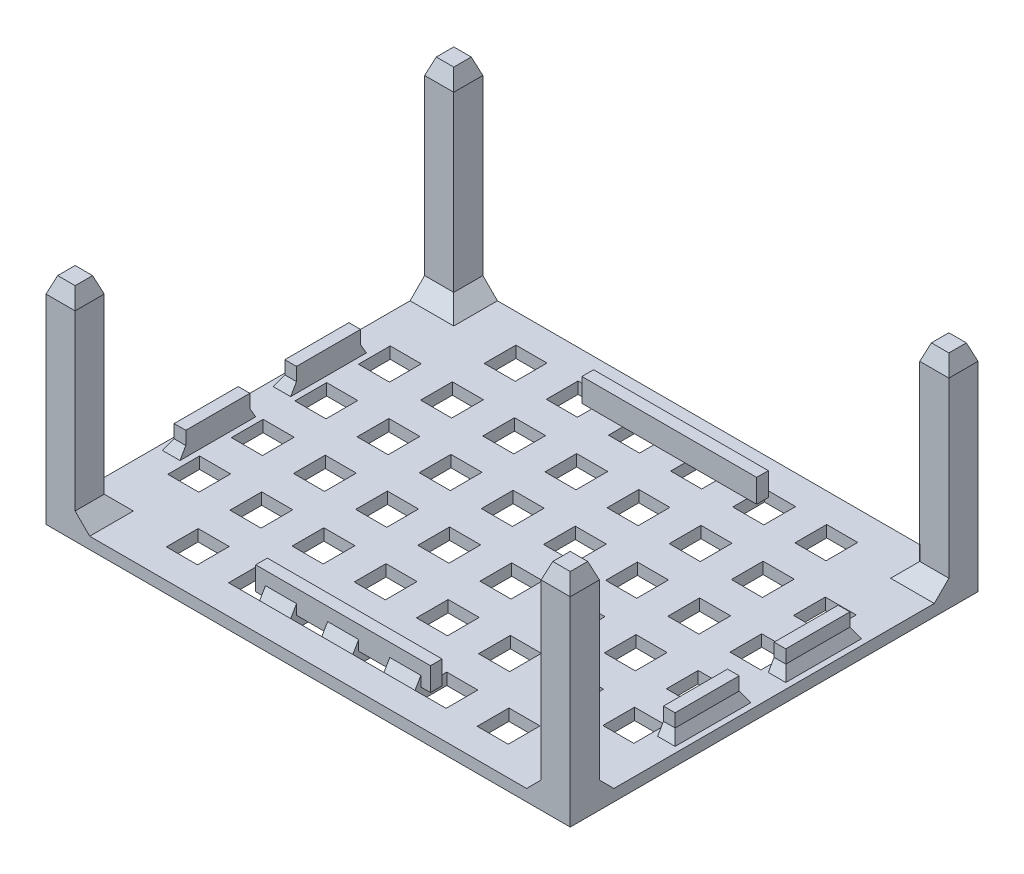
SolidWorks part; units mm, degrees
ref_plane "Plano frontal" through (0, 0, 0) normal (0, 0, 1) x (1, 0, 0)
ref_plane "Plano superior" through (0, 0, 0) normal (0, 1, 0) x (1, 0, 0)
ref_plane "Plano direito" through (0, 0, 0) normal (1, 0, 0) x (0, 0, -1)
sketch "Esboço1" plane through (0, 0, 0) normal (0, 1, 0) x (1, 0, 0)
  line L1 (-45, -35) -> (45, -35)
  line L2 (-45, -35) -> (-45, 35)
  line L3 (-45, 35) -> (45, 35)
  line L4 (45, -35) -> (45, 35)
  line L5 (-45, -35) -> (45, 35) construction
  line L6 (-45, 35) -> (45, -35) construction
  point P0 (0, 0)
  dimension "D1" = 90
  dimension "D2" = 70
extrude "Ressalto-extrusão1" add sketch "Esboço1" along normal blind 2
sketch "Esboço2" plane through (0, 2, 0) normal (0, 1, 0) x (1, 0, 0)
  line L0 (-29.33, 30) -> (-29.33, 24.55)
  line L7 (-40, 30) -> (-34.666, 30)
  line L10 (-45, 35) -> (-45, -35) construction
  line L11 (-40, -30) -> (40, -30)
  line L12 (-40, -30) -> (-40, 30)
  line L13 (-40, 30) -> (40, 30)
  line L14 (40, -30) -> (40, 30)
  line L15 (-40, -30) -> (40, 30) construction
  line L16 (-40, 30) -> (40, -30) construction
  line L17 (45, 35) -> (-45, 35) construction
  line L18 (-40, 30) -> (-40, 24.55)
  line L19 (-40, 24.55) -> (-34.666, 24.55)
  line L20 (-34.666, 30) -> (-34.666, 24.55)
  line L21 (-23.996, 30) -> (-23.996, 24.55)
  line L22 (-29.33, 30) -> (-23.996, 30)
  line L23 (-29.33, 24.55) -> (-23.996, 24.55)
  line L24 (-18.66, 30) -> (-18.66, 24.55)
  line L25 (-13.326, 30) -> (-13.326, 24.55)
  line L26 (-18.66, 30) -> (-13.326, 30)
  line L27 (-18.66, 24.55) -> (-13.326, 24.55)
  line L28 (-7.99, 30) -> (-7.99, 24.55)
  line L29 (-2.656, 30) -> (-2.656, 24.55)
  line L30 (-7.99, 30) -> (-2.656, 30)
  line L31 (-7.99, 24.55) -> (-2.656, 24.55)
  line L32 (2.68, 30) -> (2.68, 24.55)
  line L33 (8.014, 30) -> (8.014, 24.55)
  line L34 (2.68, 30) -> (8.014, 30)
  line L35 (2.68, 24.55) -> (8.014, 24.55)
  line L36 (13.35, 30) -> (13.35, 24.55)
  line L37 (18.684, 30) -> (18.684, 24.55)
  line L38 (13.35, 30) -> (18.684, 30)
  line L39 (13.35, 24.55) -> (18.684, 24.55)
  line L40 (24.02, 30) -> (24.02, 24.55)
  line L41 (29.354, 30) -> (29.354, 24.55)
  line L42 (24.02, 30) -> (29.354, 30)
  line L43 (24.02, 24.55) -> (29.354, 24.55)
  line L44 (34.69, 30) -> (34.69, 24.55)
  line L45 (40.024, 30) -> (40.024, 24.55)
  line L46 (34.69, 30) -> (40.024, 30)
  line L47 (34.69, 24.55) -> (40.024, 24.55)
  line L48 (-29.33, 19.09) -> (-29.33, 13.64)
  line L49 (-23.996, 19.09) -> (-23.996, 13.64)
  line L50 (-29.33, 19.09) -> (-23.996, 19.09)
  line L51 (-29.33, 13.64) -> (-23.996, 13.64)
  line L52 (-18.66, 19.09) -> (-18.66, 13.64)
  line L53 (-13.326, 19.09) -> (-13.326, 13.64)
  line L54 (-18.66, 19.09) -> (-13.326, 19.09)
  line L55 (-18.66, 13.64) -> (-13.326, 13.64)
  line L56 (-7.99, 19.09) -> (-7.99, 13.64)
  line L57 (-2.656, 19.09) -> (-2.656, 13.64)
  line L58 (-7.99, 19.09) -> (-2.656, 19.09)
  line L59 (-7.99, 13.64) -> (-2.656, 13.64)
  line L60 (2.68, 19.09) -> (2.68, 13.64)
  line L61 (8.014, 19.09) -> (8.014, 13.64)
  line L62 (2.68, 19.09) -> (8.014, 19.09)
  line L63 (2.68, 13.64) -> (8.014, 13.64)
  line L64 (13.35, 19.09) -> (13.35, 13.64)
  line L65 (18.684, 19.09) -> (18.684, 13.64)
  line L66 (13.35, 19.09) -> (18.684, 19.09)
  line L67 (13.35, 13.64) -> (18.684, 13.64)
  line L68 (24.02, 19.09) -> (24.02, 13.64)
  line L69 (29.354, 19.09) -> (29.354, 13.64)
  line L70 (24.02, 19.09) -> (29.354, 19.09)
  line L71 (24.02, 13.64) -> (29.354, 13.64)
  line L72 (34.69, 19.09) -> (34.69, 13.64)
  line L73 (40.024, 19.09) -> (40.024, 13.64)
  line L74 (34.69, 19.09) -> (40.024, 19.09)
  line L75 (34.69, 13.64) -> (40.024, 13.64)
  line L76 (-29.33, 8.18) -> (-29.33, 2.73)
  line L77 (-23.996, 8.18) -> (-23.996, 2.73)
  line L78 (-29.33, 8.18) -> (-23.996, 8.18)
  line L79 (-29.33, 2.73) -> (-23.996, 2.73)
  line L80 (-18.66, 8.18) -> (-18.66, 2.73)
  line L81 (-13.326, 8.18) -> (-13.326, 2.73)
  line L82 (-18.66, 8.18) -> (-13.326, 8.18)
  line L83 (-18.66, 2.73) -> (-13.326, 2.73)
  line L84 (-7.99, 8.18) -> (-7.99, 2.73)
  line L85 (-2.656, 8.18) -> (-2.656, 2.73)
  line L86 (-7.99, 8.18) -> (-2.656, 8.18)
  line L87 (-7.99, 2.73) -> (-2.656, 2.73)
  line L88 (2.68, 8.18) -> (2.68, 2.73)
  line L89 (8.014, 8.18) -> (8.014, 2.73)
  line L90 (2.68, 8.18) -> (8.014, 8.18)
  line L91 (2.68, 2.73) -> (8.014, 2.73)
  line L92 (13.35, 8.18) -> (13.35, 2.73)
  line L93 (18.684, 8.18) -> (18.684, 2.73)
  line L94 (13.35, 8.18) -> (18.684, 8.18)
  line L95 (13.35, 2.73) -> (18.684, 2.73)
  line L96 (24.02, 8.18) -> (24.02, 2.73)
  line L97 (29.354, 8.18) -> (29.354, 2.73)
  line L98 (24.02, 8.18) -> (29.354, 8.18)
  line L99 (24.02, 2.73) -> (29.354, 2.73)
  line L100 (34.69, 8.18) -> (34.69, 2.73)
  line L101 (40.024, 8.18) -> (40.024, 2.73)
  line L102 (34.69, 8.18) -> (40.024, 8.18)
  line L103 (34.69, 2.73) -> (40.024, 2.73)
  line L104 (-29.33, -2.73) -> (-29.33, -8.18)
  line L105 (-23.996, -2.73) -> (-23.996, -8.18)
  line L106 (-29.33, -2.73) -> (-23.996, -2.73)
  line L107 (-29.33, -8.18) -> (-23.996, -8.18)
  line L108 (-18.66, -2.73) -> (-18.66, -8.18)
  line L109 (-13.326, -2.73) -> (-13.326, -8.18)
  line L110 (-18.66, -2.73) -> (-13.326, -2.73)
  line L111 (-18.66, -8.18) -> (-13.326, -8.18)
  line L112 (-7.99, -2.73) -> (-7.99, -8.18)
  line L113 (-2.656, -2.73) -> (-2.656, -8.18)
  line L114 (-7.99, -2.73) -> (-2.656, -2.73)
  line L115 (-7.99, -8.18) -> (-2.656, -8.18)
  line L116 (2.68, -2.73) -> (2.68, -8.18)
  line L117 (8.014, -2.73) -> (8.014, -8.18)
  line L118 (2.68, -2.73) -> (8.014, -2.73)
  line L119 (2.68, -8.18) -> (8.014, -8.18)
  line L120 (13.35, -2.73) -> (13.35, -8.18)
  line L121 (18.684, -2.73) -> (18.684, -8.18)
  line L122 (13.35, -2.73) -> (18.684, -2.73)
  line L123 (13.35, -8.18) -> (18.684, -8.18)
  line L124 (24.02, -2.73) -> (24.02, -8.18)
  line L125 (29.354, -2.73) -> (29.354, -8.18)
  line L126 (24.02, -2.73) -> (29.354, -2.73)
  line L127 (24.02, -8.18) -> (29.354, -8.18)
  line L128 (34.69, -2.73) -> (34.69, -8.18)
  line L129 (40.024, -2.73) -> (40.024, -8.18)
  line L130 (34.69, -2.73) -> (40.024, -2.73)
  line L131 (34.69, -8.18) -> (40.024, -8.18)
  line L132 (-29.33, -13.64) -> (-29.33, -19.09)
  line L133 (-23.996, -13.64) -> (-23.996, -19.09)
  line L134 (-29.33, -13.64) -> (-23.996, -13.64)
  line L135 (-29.33, -19.09) -> (-23.996, -19.09)
  line L136 (-18.66, -13.64) -> (-18.66, -19.09)
  line L137 (-13.326, -13.64) -> (-13.326, -19.09)
  line L138 (-18.66, -13.64) -> (-13.326, -13.64)
  line L139 (-18.66, -19.09) -> (-13.326, -19.09)
  line L140 (-7.99, -13.64) -> (-7.99, -19.09)
  line L141 (-2.656, -13.64) -> (-2.656, -19.09)
  line L142 (-7.99, -13.64) -> (-2.656, -13.64)
  line L143 (-7.99, -19.09) -> (-2.656, -19.09)
  line L144 (2.68, -13.64) -> (2.68, -19.09)
  line L145 (8.014, -13.64) -> (8.014, -19.09)
  line L146 (2.68, -13.64) -> (8.014, -13.64)
  line L147 (2.68, -19.09) -> (8.014, -19.09)
  line L148 (13.35, -13.64) -> (13.35, -19.09)
  line L149 (18.684, -13.64) -> (18.684, -19.09)
  line L150 (13.35, -13.64) -> (18.684, -13.64)
  line L151 (13.35, -19.09) -> (18.684, -19.09)
  line L152 (24.02, -13.64) -> (24.02, -19.09)
  line L153 (29.354, -13.64) -> (29.354, -19.09)
  line L154 (24.02, -13.64) -> (29.354, -13.64)
  line L155 (24.02, -19.09) -> (29.354, -19.09)
  line L156 (34.69, -13.64) -> (34.69, -19.09)
  line L157 (40.024, -13.64) -> (40.024, -19.09)
  line L158 (34.69, -13.64) -> (40.024, -13.64)
  line L159 (34.69, -19.09) -> (40.024, -19.09)
  line L160 (-29.33, -24.55) -> (-29.33, -30)
  line L161 (-23.996, -24.55) -> (-23.996, -30)
  line L162 (-29.33, -24.55) -> (-23.996, -24.55)
  line L163 (-29.33, -30) -> (-23.996, -30)
  line L164 (-18.66, -24.55) -> (-18.66, -30)
  line L165 (-13.326, -24.55) -> (-13.326, -30)
  line L166 (-18.66, -24.55) -> (-13.326, -24.55)
  line L167 (-18.66, -30) -> (-13.326, -30)
  line L168 (-7.99, -24.55) -> (-7.99, -30)
  line L169 (-2.656, -24.55) -> (-2.656, -30)
  line L170 (-7.99, -24.55) -> (-2.656, -24.55)
  line L171 (-7.99, -30) -> (-2.656, -30)
  line L172 (2.68, -24.55) -> (2.68, -30)
  line L173 (8.014, -24.55) -> (8.014, -30)
  line L174 (2.68, -24.55) -> (8.014, -24.55)
  line L175 (2.68, -30) -> (8.014, -30)
  line L176 (13.35, -24.55) -> (13.35, -30)
  line L177 (18.684, -24.55) -> (18.684, -30)
  line L178 (13.35, -24.55) -> (18.684, -24.55)
  line L179 (13.35, -30) -> (18.684, -30)
  line L180 (24.02, -24.55) -> (24.02, -30)
  line L181 (29.354, -24.55) -> (29.354, -30)
  line L182 (24.02, -24.55) -> (29.354, -24.55)
  line L183 (24.02, -30) -> (29.354, -30)
  line L184 (34.69, -24.55) -> (34.69, -30)
  line L185 (40.024, -24.55) -> (40.024, -30)
  line L186 (34.69, -24.55) -> (40.024, -24.55)
  line L187 (34.69, -30) -> (40.024, -30)
  line L188 (-40, 19.09) -> (-40, 13.64)
  line L189 (-34.666, 19.09) -> (-34.666, 13.64)
  line L190 (-40, 19.09) -> (-34.666, 19.09)
  line L191 (-40, 13.64) -> (-34.666, 13.64)
  line L192 (-40, 8.18) -> (-40, 2.73)
  line L193 (-34.666, 8.18) -> (-34.666, 2.73)
  line L194 (-40, 8.18) -> (-34.666, 8.18)
  line L195 (-40, 2.73) -> (-34.666, 2.73)
  line L196 (-40, -2.73) -> (-40, -8.18)
  line L197 (-34.666, -2.73) -> (-34.666, -8.18)
  line L198 (-40, -2.73) -> (-34.666, -2.73)
  line L199 (-40, -8.18) -> (-34.666, -8.18)
  line L200 (-40, -13.64) -> (-40, -19.09)
  line L201 (-34.666, -13.64) -> (-34.666, -19.09)
  line L202 (-40, -13.64) -> (-34.666, -13.64)
  line L203 (-40, -19.09) -> (-34.666, -19.09)
  line L204 (-40, -24.55) -> (-40, -30)
  line L205 (-34.666, -24.55) -> (-34.666, -30)
  line L206 (-40, -24.55) -> (-34.666, -24.55)
  line L207 (-40, -30) -> (-34.666, -30)
  point P0 (0, 0)
  dimension "D1" = 5
  dimension "D2" = 5
  dimension "D3" = 5.334
  dimension "D4" = 5.45
  dimension "D5" = 6
sketch "Esboço3" plane through (0, 2, 0) normal (0, 1, 0) x (1, 0, 0)
  line L0 (40, 35) -> (45, 35)
  line L5 (-45, 35) -> (-40, 35)
  line L6 (-45, 35) -> (-45, 30)
  line L7 (-45, 30) -> (-40, 30)
  line L8 (-40, 35) -> (-40, 30)
  line L9 (45, 35) -> (45, 30)
  line L10 (40, 30) -> (45, 30)
  line L11 (40, 35) -> (40, 30)
  line L12 (40, -30) -> (45, -30)
  line L13 (45, -30) -> (45, -35)
  line L14 (40, -35) -> (45, -35)
  line L15 (40, -30) -> (40, -35)
  line L16 (-45, -30) -> (-40, -30)
  line L17 (-40, -30) -> (-40, -35)
  line L18 (-45, -35) -> (-40, -35)
  line L19 (-45, -30) -> (-45, -35)
  dimension "D1" = 5
  dimension "D2" = 5
  dimension "D3" = 2
extrude "Ressalto-extrusão2" add sketch "Esboço3" along normal blind 35
sketch "Esboço4" plane through (0, 2, 0) normal (0, 1, 0) x (1, 0, 0)
  line L0 (0, 35) -> (0, -35) construction
  line L1 (40, 35) -> (-40, 35) construction
  line L2 (-40, -35) -> (40, -35) construction
  line L3 (-45, 0) -> (45, 0) construction
  line L4 (-15, 27) -> (15, 27)
  line L5 (-15, 27) -> (-15, 29)
  line L6 (-15, 29) -> (15, 29)
  line L7 (15, 27) -> (15, 29)
  line L8 (-15, 27) -> (15, 29) construction
  line L9 (-15, 29) -> (15, 27) construction
  line L10 (-15, -27) -> (15, -27)
  line L11 (-15, -27) -> (-15, -29)
  line L12 (-15, -29) -> (15, -29)
  line L13 (15, -27) -> (15, -29)
  line L14 (-15, -27) -> (15, -29) construction
  line L15 (-15, -29) -> (15, -27) construction
  line L16 (-45, 30) -> (-45, -30) construction
  line L17 (45, -30) -> (45, 30) construction
  line L18 (43, 4) -> (43, 15)
  line L25 (41, -15) -> (43, -15)
  line L26 (41, -15) -> (41, -4)
  line L27 (41, 15) -> (43, 15)
  line L28 (43, -15) -> (43, -4)
  line L29 (41, -15) -> (43, 15) construction
  line L30 (41, 15) -> (43, -15) construction
  line L37 (41, -4) -> (43, -4)
  line L39 (41, 4) -> (43, 4)
  line L41 (41, -4) -> (43, 4) construction
  line L42 (41, 4) -> (43, -4) construction
  line L43 (41, 4) -> (41, 15)
  line L50 (-41, 4) -> (-41, 15)
  line L51 (-43, -15) -> (-41, -15)
  line L52 (-43, -15) -> (-43, -4)
  line L53 (-43, 15) -> (-41, 15)
  line L54 (-41, -15) -> (-41, -4)
  line L55 (-43, -4) -> (-41, -4)
  line L56 (-43, 4) -> (-41, 4)
  line L57 (-43, 4) -> (-43, 15)
  line L58 (-43, -15) -> (-41, 15) construction
  line L59 (-43, 15) -> (-41, -15) construction
  line L60 (-43, -4) -> (-41, 4) construction
  line L61 (-43, 4) -> (-41, -4) construction
  point P6 (0, 28)
  point P11 (0, -28)
  point P17 (-42, 0)
  point P28 (-42, 0)
  point P30 (42, 0)
  point P40 (42, 0)
  dimension "D2" = 2
  dimension "D3" = 2
  dimension "D4" = 30
  dimension "D5" = 30
  dimension "D6" = 27
  dimension "D10" = 2
  dimension "D11" = 54
  dimension "D12" = 30
  dimension "D14" = 8
extrude "Ressalto-extrusão4" add sketch "Esboço4" along normal blind 4
extrude "Corte-extrusão2" cut sketch "Esboço2" against normal through all contours L0 L23 L21 L13 | L12 L191 L189 L190 | L48 L51 L49 L50 | L12 L195 L193 L194 | L76 L79 L77 L78 | L12 L199 L197 L198 | L104 L107 L105 L106 | L12 L203 L201 L202 | L132 L135 L133 L134 | L136 L139 L137 L138 | L108 L111 L109 L110 | L80 L83 L81 L82 | L52 L55 L53 L54 | L24 L27 L25 L13 | L28 L31 L29 L13 | L56 L59 L57 L58 | L84 L87 L85 L86 | L112 L115 L113 L114 | L140 L143 L141 L142 | L144 L147 L145 L146 | L116 L119 L117 L118 | L88 L91 L89 L90 | L60 L63 L61 L62 | L32 L35 L33 L13 | L36 L39 L37 L13 | L64 L67 L65 L66 | L92 L95 L93 L94 | L120 L123 L121 L122 | L148 L151 L149 L150 | L152 L155 L153 L154 | L124 L127 L125 L126 | L96 L99 L97 L98 | L68 L71 L69 L70 | L40 L43 L41 L13 | L72 L75 L14 L74 | L100 L103 L14 L102 | L128 L131 L14 L130 | L156 L159 L14 L158 | L162 L160 L11 L161 | L166 L164 L11 L165 | L170 L168 L11 L169 | L174 L172 L11 L173 | L178 L176 L11 L177 | L182 L180 L11 L181
chamfer "Chanfro1" distance 1 angle 70 16 edges at (42.5, 37, 30) (45, 37, 32.5) (42.5, 37, 35) (40, 37, 32.5) (42.5, 37, -35) (45, 37, -32.5) (42.5, 37, -30) (40, 37, -32.5) (-42.5, 37, 30) (-40, 37, 32.5) (-42.5, 37, 35) (-45, 37, 32.5) (-42.5, 37, -35) (-40, 37, -32.5) (-42.5, 37, -30) (-45, 37, -32.5)
chamfer "Chanfro2" distance 2.5 angle 45 8 edges at (-40, 2, 32.5) (-42.5, 2, 30) (42.5, 2, 30) (40, 2, 32.5) (40, 2, -32.5) (42.5, 2, -30) (-40, 2, -32.5) (-42.5, 2, -30)
chamfer "Chanfro3" distance 1 angle 60 18 edges at (-10.658, 2, -29) (0.012, 2, -29) (10.682, 2, -29) (-42, 2, -15) (-43, 2, -9.5) (-42, 2, -4) (-42, 2, 4) (-43, 2, 9.5) (-42, 2, 15) (42, 2, -15) (42, 2, -4) (43, 2, -9.5) (42, 2, 4) (42, 2, 15) (43, 2, 9.5) (10.682, 2, 29) (-10.658, 2, 29) (0.012, 2, 29)
